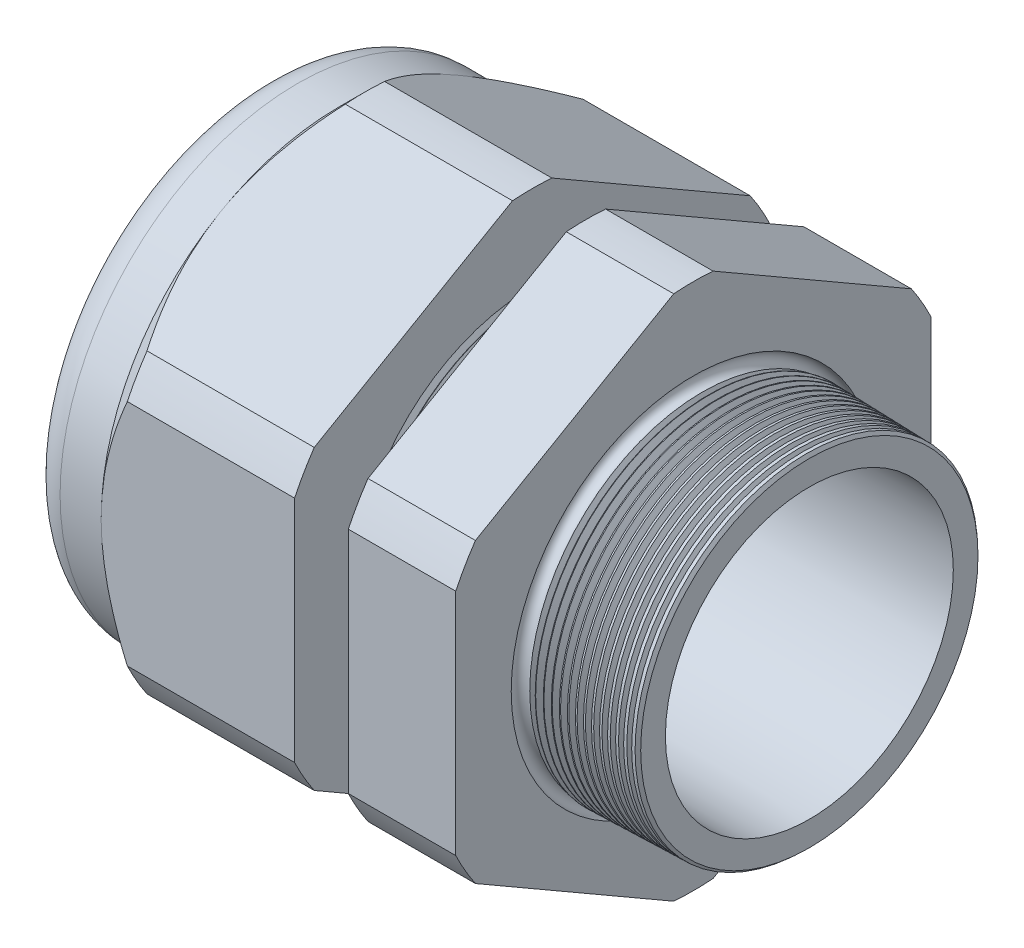
SolidWorks part; units mm, degrees
ref_plane "Front Plane" through (0, 0, 0) normal (0, 0, 1) x (1, 0, 0)
ref_plane "Top Plane" through (0, 0, 0) normal (0, 1, 0) x (1, 0, 0)
ref_plane "Right Plane" through (0, 0, 0) normal (1, 0, 0) x (0, 0, -1)
sketch "Sketch10" plane through (0, 0, 0) normal (0, 0, 1) x (1, 0, 0)
  line L0 (0, 0) -> (-115.3565, 0) construction
  line L1 (-55.88, 16.002) -> (-25.8776, 16.002)
  line L2 (5.08, 16.0803) -> (5.08, 19.1283)
  line L3 (-7.874, 19.4676) -> (5.08, 19.1283)
  line L4 (-7.874, 53.086) -> (-7.874, 19.4676)
  line L5 (-7.874, 53.086) -> (-19.874, 53.086)
  line L6 (-19.874, 53.086) -> (-19.874, 19.7818)
  line L7 (-25.8776, 19.939) -> (-19.874, 19.7818)
  line L8 (-25.8776, 19.939) -> (-25.8776, 53.086)
  line L9 (-25.8776, 53.086) -> (-47.48, 53.086)
  line L10 (-47.48, 53.086) -> (-47.48, 26.543)
  line L11 (-47.48, 26.543) -> (-55.88, 26.543)
  line L12 (-55.88, 26.543) -> (-55.88, 16.002)
  line L13 (-25.8776, 16.002) -> (5.08, 16.0803)
  dimension "D1" = 60.96
  dimension "D2" = 32.004
  dimension "D3" = 1.5
  dimension "D4" = 3.048
  dimension "A" = 39.878
  dimension "D6" = 53.086
  dimension "D8" = 106.172
  dimension "D9" = 8.4
  dimension "D10" = 21.6024
  dimension "D11" = 12
  dimension "D" = 12.954
revolve "Revolve2" add sketch "Sketch10" angle 360 about L0
sketch "Sketch12" plane through (-47.48, 0, 0) normal (-1, 0, 0) x (0, 0, 1)
  line L1 (-2.1972, 29.3807) -> (-24.3458, 16.5931)
  line L2 (-26.543, 12.7876) -> (-26.543, -12.7876)
  line L3 (-24.3458, -16.5931) -> (-2.1972, -29.3807)
  line L4 (2.1972, -29.3807) -> (24.3458, -16.5931)
  line L5 (26.543, -12.7876) -> (26.543, 12.7876)
  line L6 (24.3458, 16.5931) -> (2.1972, 29.3807)
  circle A0 centre (0, 0) radius 26.543 construction
  arc A1 (2.1972, 29.3807) -> (-2.1972, 29.3807) centre (0, 0) ccw
  arc A2 (-24.3458, 16.5931) -> (-26.543, 12.7876) centre (0, 0) ccw
  arc A3 (-26.543, -12.7876) -> (-24.3458, -16.5931) centre (0, 0) ccw
  arc A4 (-2.1972, -29.3807) -> (2.1972, -29.3807) centre (0, 0) ccw
  arc A5 (24.3458, -16.5931) -> (26.543, -12.7876) centre (0, 0) ccw
  arc A6 (26.543, 12.7876) -> (24.3458, 16.5931) centre (0, 0) ccw
  dimension "D2" = 58.9255
  dimension "D1" = 53.086
extrude "Cut-Extrude2" cut sketch "Sketch12" against normal through all flip side to cut
fillet "Fillet4" radius 3.81 1 edges at (-55.88, 0, -26.543)
sketch "Sketch19" plane through (-47.48, 0, 0) normal (-1, 0, 0) x (0, 0, 1)
  line L0 (26.543, 0) -> (26.543, 12.7876) construction
  circle A0 centre (0, 0) radius 26.543
extrude "Cut-Extrude3" cut sketch "Sketch19" against normal blind 3.998 draft 45 flip side to cut
chamfer "Chamfer1" distance 0.254 angle 45 1 edges at (5.08, 0, -19.1283)
sketch "Sketch21" plane through (-55.88, 0, 0) normal (-1, 0, 0) x (0, 0, 1)
  circle A0 centre (0, 0) radius 16.002
  circle A2 centre (0, 0) radius 16.002 construction
extrude "plug" add sketch "Sketch21" against normal blind 12.7 separate body
sketch "Sketch22" plane through (-55.88, 0, 0) normal (-1, 0, 0) x (0, 0, 1)
  circle A0 centre (0, 0) radius 15.748
  circle A1 centre (0, 0) radius 16.002 construction
  dimension "D1" = 0.254
extrude "Cut-Extrude4" cut sketch "Sketch22" against normal blind 0.508
sketch "Sketch27" plane through (-55.372, 0, 0) normal (-1, 0, 0) x (0, 0, 1)
  line L0 (-4.3624, 0) -> (4.3624, 0) construction
  circle A0 centre (-11.7953, 0) radius 3.937
  circle A1 centre (0, 0) radius 15.748 construction
  dimension "D1" = 0.0157
  dimension "holedia" = 7.874
extrude "plugholes" cut sketch "Sketch27" against normal through all
pattern_circular "CirPattern1" count 6 over 360 about axis through (0, 0, 0) along (1, 0, 0) of "plugholes"
sketch "Sketch28" [suppressed] plane through (-38.354, 0, 0) normal (-1, 0, 0) x (0, 0, 1)
  circle A0 centre (0, 0) radius 1.905
  dimension "midholedia" = 7.874
extrude "midhole" [suppressed] cut sketch "Sketch28" against normal through all
sketch "Sketch29" plane through (0, 0, 0) normal (0, 0, 1) x (1, 0, 0)
  line L0 (-25.8776, 19.939) -> (-25.1446, 19.9198)
  line L1 (-19.874, 19.7818) -> (-25.8776, 19.939) construction
  line L2 (-25.1446, 19.9198) -> (-25.5277, 19.2946)
  line L3 (-25.5277, 19.2946) -> (-25.8776, 19.939)
  dimension "D1" = 60
  dimension "D2" = 60
  dimension "D3" = 0.635
revolve "Cut-Revolve1" cut sketch "Sketch29" angle 360 about axis through (0, 0, 0) along (-1, 0, 0)
pattern_linear "LPattern1" count 8 spacing 0.762 along (1, 0, 0) of "Cut-Revolve1"
sketch "Sketch30" plane through (0, 0, 0) normal (0, 0, 1) x (1, 0, 0)
  line L0 (-7.874, 19.4676) -> (-6.9944, 19.4445)
  line L1 (-7.874, 29.3807) -> (-7.874, 16.5931) construction
  line L2 (4.8261, 19.135) -> (-7.874, 19.4676) construction
  line L3 (-6.9944, 19.4445) -> (-7.4542, 18.6943)
  line L4 (-7.4542, 18.6943) -> (-7.874, 19.4676)
  dimension "D1" = 60
  dimension "D2" = 60
  dimension "D3" = 0.762
revolve "Cut-Revolve2" cut sketch "Sketch30" angle 360 about axis through (0, 0, 0) along (-1, 0, 0)
pattern_linear "LPattern2" count 15 spacing 0.889 along (1, 0, 0) of "Cut-Revolve2"
sketch "Sketch31" [suppressed] plane through (-38.354, 0, 0) normal (-1, 0, 0) x (0, 0, 1)
  line L0 (-1.905, 1.905) -> (1.905, 1.905)
  line L1 (-1.905, -1.905) -> (1.905, -1.905)
  circle A0 centre (0, 0) radius 1.905 construction
  arc A1 (-1.905, 1.905) -> (-1.905, -1.905) centre (-1.905, 0) ccw
  arc A2 (1.905, 1.905) -> (1.905, -1.905) centre (1.905, 0) cw
extrude "Cut-Extrude5" [suppressed] cut sketch "Sketch31" against normal through all
sketch "Sketch32" plane through (0, 0, 0) normal (0, 0, 1) x (1, 0, 0)
  line L0 (-7.874, 29.3807) -> (-7.874, 16.5931) construction
  circle A0 centre (-7.747, 19.4676) radius 0.889
  dimension "D2" = 1.778
  dimension "D1" = 0.127
revolve "Cut-Revolve3" cut sketch "Sketch32" angle 360 about axis through (0, 0, 0) along (-1, 0, 0)
